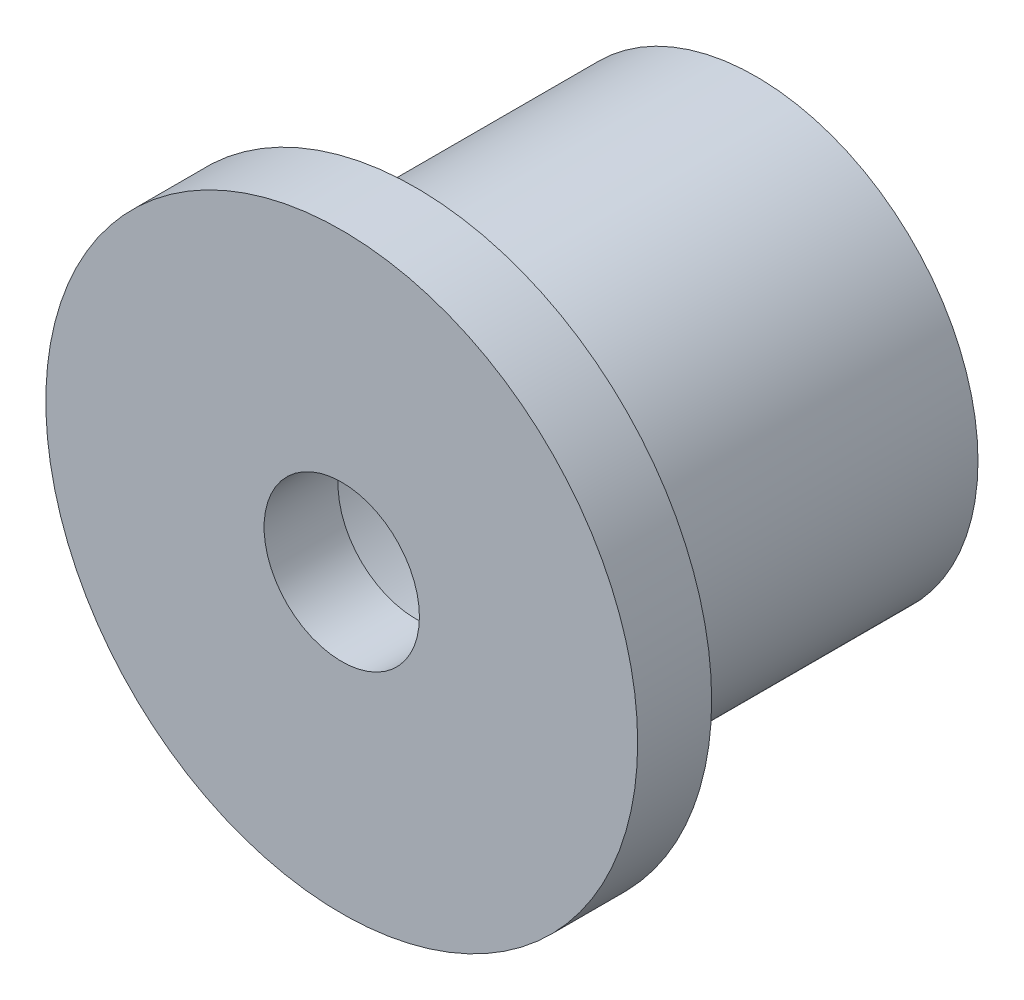
SolidWorks part; units mm, degrees
material "AISI 1020"
ref_plane "Спереди" through (0, 0, 0) normal (0, 0, 1) x (1, 0, 0)
ref_plane "Сверху" through (0, 0, 0) normal (0, 1, 0) x (1, 0, 0)
ref_plane "Справа" through (0, 0, 0) normal (1, 0, 0) x (0, 0, -1)
sketch "Эскиз1" plane through (0, 0, 0) normal (1, 0, 0) x (0, 0, -1)
  line L0 (-1000, 0) -> (49000, 0) construction
  line L1 (0, 12.5) -> (-23, 12.5)
  line L2 (-3, 20) -> (-23, 20) construction
  line L3 (-3, 20) -> (-3, -20) construction
  line L4 (-3, -20) -> (-23, -20) construction
  line L5 (-23, 20) -> (-23, -20) construction
  line L6 (-23, 12.5) -> (-23, 5.25)
  line L7 (-23, 5.25) -> (-28, 5.25)
  line L8 (-28, 5.25) -> (-28, 20)
  line L9 (-28, 20) -> (-23, 20)
  line L10 (-23, 20) -> (-23, 15)
  line L11 (-23, 15) -> (0, 15)
  line L12 (0, 15) -> (0, 12.5)
  line L13 (63, 12.5) -> (-23, 12.5) construction
  point P7 (-23, 0)
  dimension "D1" = 3
  dimension "D2" = 20
  dimension "D3" = 40
  dimension "D4" = 10.5
  dimension "D5" = 40
  dimension "D6" = 5
  dimension "D7" = 30
  dimension "D8" = 3
revolve "Повернуть1" add sketch "Эскиз1" angle 360 about L0
